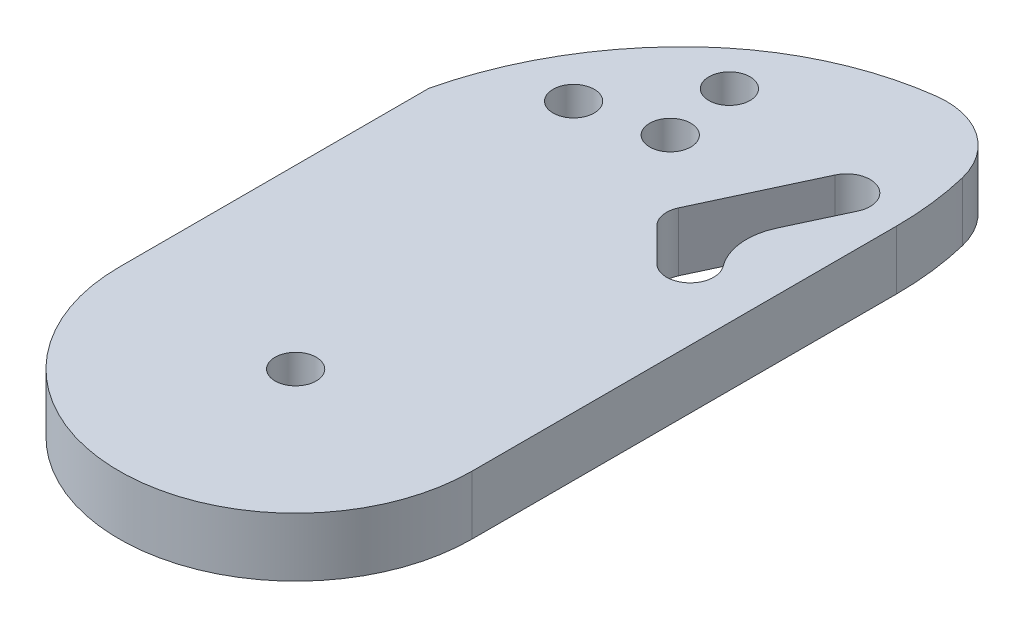
SolidWorks part; units mm, degrees
ref_plane "Front Plane" through (0, 0, 0) normal (0, 0, 1) x (1, 0, 0)
ref_plane "Top Plane" through (0, 0, 0) normal (0, 1, 0) x (1, 0, 0)
ref_plane "Right Plane" through (0, 0, 0) normal (1, 0, 0) x (0, 0, -1)
sketch "Sketch1" plane through (0, 0, 0) normal (0, 1, 0) x (1, 0, 0)
  line L0 (0, 0) -> (0, 50) construction
  line L1 (-15, 0) -> (-15, 50)
  line L2 (15, 0) -> (15, 50)
  line L3 (10.4451, 36.3547) -> (6.2189, 27.2917) construction
  line L4 (12.2577, 35.5095) -> (8.6234, 27.7156)
  line L5 (8.6325, 37.2) -> (4.4063, 28.1369)
  line L6 (0, 65) -> (0, 60) construction
  line L7 (0, 60) -> (-6.5, 48.7417) construction
  line L8 (-6.5, 48.7417) -> (6.5, 48.7417) construction
  line L9 (6.5, 48.7417) -> (0, 60) construction
  line L10 (6.2189, 27.2917) -> (9, 24.5106) construction
  line L11 (8.6234, 27.7156) -> (10.4142, 25.9248)
  line L12 (4.8047, 25.8774) -> (7.5858, 23.0964)
  arc A0 (-15, 0) -> (15, 0) centre (0, 0) ccw
  arc A1 (15, 50) -> (-15, 50) centre (0, 50) ccw
  circle A2 centre (0, 0) radius 1.75
  arc A3 (12.2577, 35.5095) -> (8.6325, 37.2) centre (10.4451, 36.3547) ccw
  arc A4 (4.4063, 28.1369) -> (4.8047, 25.8774) centre (6.2189, 27.2917) ccw
  circle A5 centre (0, 60) radius 3.175 construction
  circle A6 centre (-6.5, 48.7417) radius 3.175 construction
  circle A7 centre (6.5, 48.7417) radius 3.175 construction
  arc A9 (4.4063, 28.1369) -> (4.8047, 25.8774) centre (6.2189, 27.2917) ccw
  arc A10 (7.5858, 23.0964) -> (10.4142, 25.9248) centre (9, 24.5106) ccw
  point P3 (0, 25)
  point P12 (6.2189, 27.2917)
  point P24 (5.4964, 12.8256)
  dimension "D1" = 15
  dimension "D2" = 3.5
  dimension "D4" = 2
  dimension "D7" = 6.35
  dimension "D8" = 5
  dimension "D12" = 110
  dimension "D3" = 50
  dimension "D5" = 25
  dimension "D6" = 10
  dimension "D9" = 13
  dimension "D10" = 13
  dimension "D11" = 6
  dimension "D13" = 13.6453
extrude "Boss-Extrude1" add sketch "Sketch1" along normal blind 5 contours L2 A1 L1 A0 A10 L12 A4 L5 A3 L4 L11 A7 A6 A5 A2
fillet "Fillet1" radius 5 1 edges at (8.6234, 2.5, -27.7156)
sketch "Sketch2" plane through (0, 5, 0) normal (0, 1, 0) x (1, 0, 0)
  line L0 (15, 0) -> (15, 50) construction
  line L2 (-15, 0) -> (-15, 50) construction
  line L3 (-15, 26.3246) -> (-40.9256, 69.2382)
  line L4 (-40.9256, 69.2382) -> (-58.772, 111.0807)
  line L5 (-58.772, 111.0807) -> (39.2844, 102.8258)
  line L6 (39.2844, 102.8258) -> (15, 36.047)
  arc A0 (15, 36.047) -> (14.2432, 42.3998) centre (-12.0434, 36.047) ccw
  arc A1 (14.2432, 42.3998) -> (7.1271, 47.2922) centre (7.9593, 40.8811) ccw
  arc A2 (7.1271, 47.2922) -> (-6.484, 40.9149) centre (10.3077, 22.7899) ccw
  arc A3 (-6.484, 40.9149) -> (-15, 26.3246) centre (13.2458, 19.6186) ccw
extrude "Cut-Extrude1" cut sketch "Sketch2" against normal blind 10
sketch "Sketch3" plane through (0, 5, 0) normal (0, 1, 0) x (1, 0, 0)
  circle A0 centre (6.1014, 47.3659) radius 3.81 construction
  circle A1 centre (-1.3018, 33.1261) radius 1.75
  circle A2 centre (3.3822, 36.8758) radius 1.75 construction
  circle A3 centre (-2.2071, 39.0574) radius 1.75
  circle A4 centre (-7.9059, 31.5198) radius 1.75
  dimension "D1" = 7.62
  dimension "D2" = 3.5
  dimension "D7" = 3.5
  dimension "D3" = 10
  dimension "D4" = 6
  dimension "D5" = 6
  dimension "D6" = 6
extrude "Cut-Extrude2" cut sketch "Sketch3" against normal blind 10
